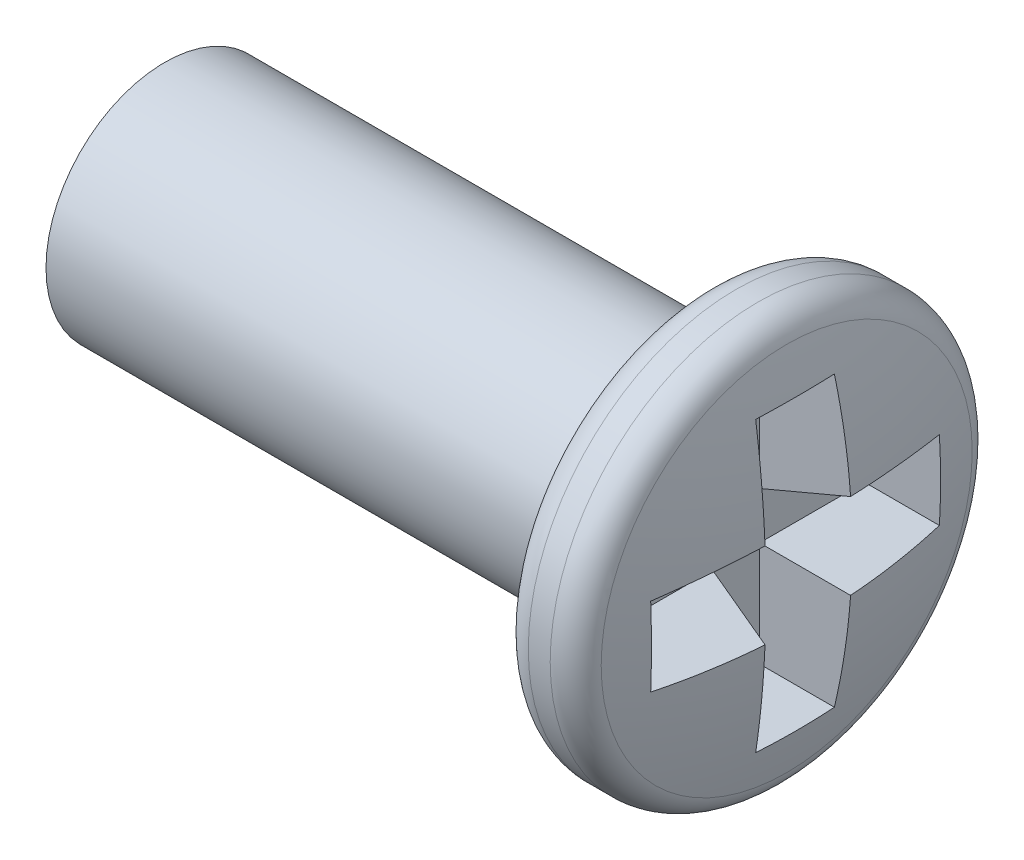
SolidWorks part; units mm, degrees
ref_plane "Front Plane" through (0, 0, 0) normal (0, 0, 1) x (1, 0, 0)
ref_plane "Top Plane" through (0, 0, 0) normal (0, 1, 0) x (1, 0, 0)
ref_plane "Right Plane" through (0, 0, 0) normal (1, 0, 0) x (0, 0, -1)
sketch "Sketch1" plane through (0, 0, 0) normal (0, 0, 1) x (1, 0, 0)
  line L0 (0, 0) -> (4.35, 0)
  line L1 (4.15, 1.4) -> (3.65, 1.4)
  line L2 (3.65, 1.4) -> (3.65, 0.8)
  line L3 (3.65, 0.8) -> (0, 0.8)
  line L4 (0, 0.8) -> (0, 0)
  line L5 (-102.0382, 0) -> (4999.8703, 0) construction
  arc A0 (4.35, 0) -> (4.15, 1.4) centre (-0.65, 0) ccw
  dimension "D1" = 1.6
  dimension "D2" = 0.7
  dimension "D3" = 4.35
  dimension "D4" = 2.8
  dimension "D5" = 0.5
revolve "Revolve1" add sketch "Sketch1" angle 360 about L5
fillet "Fillet1" radius 0.2 2 edges at (3.65, 0, 1.4) (4.15, 0, 1.4)
ref_plane "Plane1" through (4.35, 0, 0) normal (1, 0, 0) x (0, 0, -1)
sketch "Sketch2" plane through (4.35, 0, 0) normal (1, 0, 0) x (0, 0, -1)
  line L1 (0.2927, 1) -> (0.2927, 0.2927)
  line L2 (0.2927, 0.2927) -> (1, 0.2927)
  line L3 (1, 0.2927) -> (1, -0.2927)
  line L4 (1, -0.2927) -> (0.2927, -0.2927)
  line L5 (0.2927, -0.2927) -> (0.2927, -1)
  line L6 (0.2927, -1) -> (-0.2927, -1)
  line L7 (-0.2927, -1) -> (-0.2927, -0.2927)
  line L8 (-0.2927, -0.2927) -> (-1, -0.2927)
  line L9 (-1, -0.2927) -> (-1, 0.2927)
  line L10 (-1, 0.2927) -> (-0.2927, 0.2927)
  line L11 (-0.2927, 0.2927) -> (-0.2927, 1)
  line L12 (-0.2927, 1) -> (0.2927, 1)
  point P0 (0, 1)
  point P1 (1, 0)
  dimension "D1" = 2
extrude "Cut-Extrude1" cut sketch "Sketch2" against normal blind 0.5 draft 15
